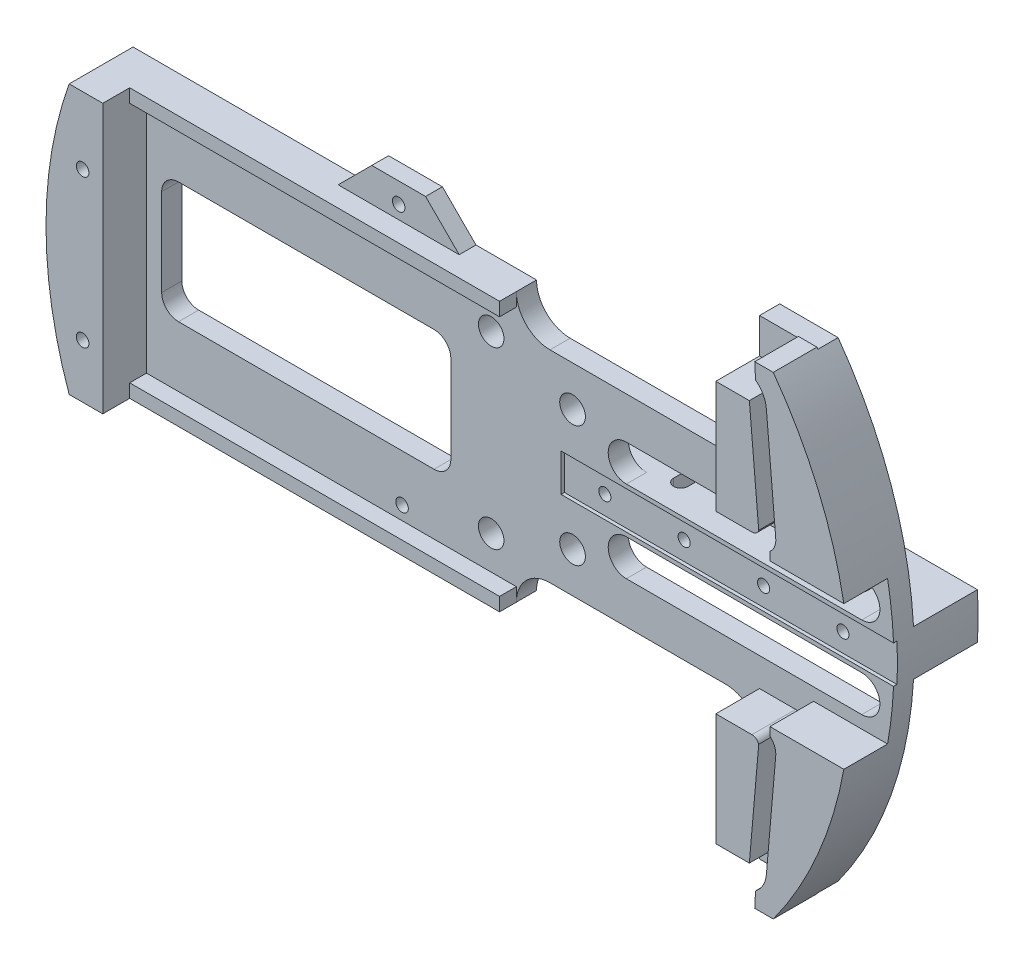
SolidWorks part; units mm, degrees
material "ABS"
ref_plane "Front Plane" through (0, 0, 0) normal (0, 0, 1) x (1, 0, 0)
ref_plane "Top Plane" through (0, 0, 0) normal (0, 1, 0) x (1, 0, 0)
ref_plane "Right Plane" through (0, 0, 0) normal (1, 0, 0) x (0, 0, -1)
sketch "Sketch1" plane through (0, 0, 0) normal (0, 0, 1) x (1, 0, 0)
  line L0 (0, 0) -> (91.8237, 0) construction
  line L1 (10.9774, 19.05) -> (44.196, 19.05)
  line L2 (-71.5726, 25.4) -> (4.6274, 25.4)
  line L3 (10.9774, -19.05) -> (44.196, -19.05)
  line L6 (50.546, 44.45) -> (61.5792, 44.45)
  line L7 (50.546, -44.45) -> (61.5792, -44.45)
  line L11 (-71.5726, -25.4) -> (4.6274, -25.4)
  line L12 (50.546, 25.4) -> (50.546, 44.45)
  line L14 (50.546, -25.4) -> (50.546, -44.45)
  arc A0 (61.5792, -44.45) -> (61.5792, 44.45) centre (0, 0) ccw
  circle A1 centre (0, 0) radius 75.946 construction
  arc A2 (-71.5726, 25.4) -> (-71.5726, -25.4) centre (0, 0) ccw
  arc A3 (44.196, 19.05) -> (50.546, 25.4) centre (44.196, 25.4) ccw
  arc A4 (10.9774, 19.05) -> (4.6274, 25.4) centre (10.9774, 25.4) cw
  arc A5 (44.196, -19.05) -> (50.546, -25.4) centre (44.196, -25.4) cw
  arc A6 (10.9774, -19.05) -> (4.6274, -25.4) centre (10.9774, -25.4) ccw
  point P6 (75.946, 0)
  point P17 (0, 0)
  dimension "D1" = 75.946
  dimension "D8" = 151.892
  dimension "D11" = 75.946
  dimension "D2" = 76.2
  dimension "D3" = 6.35
  dimension "D4" = 25.4
  dimension "D5" = 50.8
  dimension "D6" = 88.9
  dimension "D7" = 6.35
  dimension "D9" = 6.35
  dimension "D10" = 6.35
extrude "Boss-Extrude1" add sketch "Sketch1" along normal blind 3.81
sketch "Sketch2" plane through (0, 0, 3.81) normal (0, 0, 1) x (1, 0, 0)
  line L0 (60.2463, 17.78) -> (56.2059, 64.1603) construction
  line L1 (-13.9228, 0) -> (116.9939, 0) construction
  line L2 (35.7924, 17.78) -> (109.7023, 17.78) construction
  line L3 (61.8653, 17.78) -> (60.0951, 38.1)
  line L4 (58.6516, 17.5) -> (56.8815, 37.82)
  line L5 (56.8815, 37.82) -> (50.546, 37.82)
  line L6 (58.0471, 41.7789) -> (57.9008, 44.704)
  line L7 (57.9008, 44.704) -> (61.395, 44.704)
  line L8 (50.546, 37.82) -> (50.546, 16.5667)
  line L9 (50.546, 16.5667) -> (57.3661, 16.5667)
  line L10 (60.7595, 15.0941) -> (60.7595, 13.5449)
  line L11 (60.7595, 13.5449) -> (74.7284, 13.5449)
  line L12 (60.2463, -17.78) -> (56.2059, -64.1603) construction
  line L13 (60.7595, -13.5449) -> (74.7284, -13.5449)
  line L14 (60.7595, -15.0941) -> (60.7595, -13.5449)
  line L15 (50.546, -16.5667) -> (57.3661, -16.5667)
  line L16 (50.546, -37.82) -> (50.546, -16.5667)
  line L17 (57.9008, -44.704) -> (61.395, -44.704)
  line L18 (58.0471, -41.7789) -> (57.9008, -44.704)
  line L19 (56.8815, -37.82) -> (50.546, -37.82)
  line L20 (58.6516, -17.5) -> (56.8815, -37.82)
  line L21 (61.8653, -17.78) -> (60.0951, -38.1)
  line L22 (96.3863, 0) -> (96.3863, 82.276) construction
  arc A0 (61.5792, -44.45) -> (61.5792, 44.45) centre (0, 0) ccw construction
  arc A1 (60.0951, 38.1) -> (58.0471, 41.7789) centre (54.9639, 37.653) ccw
  arc A2 (57.3661, 16.5667) -> (58.6516, 17.5) centre (57.3661, 17.9187) ccw
  arc A3 (61.8653, 17.78) -> (60.7595, 15.0941) centre (58.7167, 17.5057) cw
  arc A4 (74.7284, 13.5449) -> (61.395, 44.704) centre (0, 0) ccw
  arc A5 (74.7284, -13.5449) -> (61.395, -44.704) centre (0, 0) cw
  arc A6 (61.8653, -17.78) -> (60.7595, -15.0941) centre (58.7167, -17.5057) ccw
  arc A7 (57.3661, -16.5667) -> (58.6516, -17.5) centre (57.3661, -17.9187) cw
  arc A8 (60.0951, -38.1) -> (58.0471, -41.7789) centre (54.9639, -37.653) cw
  point P0 (75.946, 0)
  point P1 (60.2463, 17.78)
  point P49 (96.3863, 44.704)
  dimension "D6" = 75.946
  dimension "D1" = 17.78
  dimension "D2" = 15.6997
  dimension "D3" = 85.021
  dimension "D4" = 1.6129
  dimension "D5" = 20.32
  dimension "D7" = 44.704
  dimension "D8" = 44.704
  dimension "D9" = 25.4
extrude "Boss-Extrude2" add sketch "Sketch2" along normal blind 8.255
sketch "Sketch3" plane through (0, 0, 3.81) normal (0, 0, 1) x (1, 0, 0)
  line L0 (-6.3906, 0) -> (92.2963, 0) construction
  line L2 (13.081, -3.55) -> (76.581, -3.55)
  line L3 (13.081, -3.55) -> (13.081, 3.55)
  line L4 (13.081, 3.55) -> (76.581, 3.55)
  line L5 (76.581, -3.55) -> (76.581, 3.55)
  line L6 (13.081, -3.55) -> (76.581, 3.55) construction
  line L7 (13.081, 3.55) -> (76.581, -3.55) construction
  line L8 (50.546, 16.5667) -> (50.546, 25.4) construction
  point P3 (44.831, 0)
  dimension "D1" = 7.1
  dimension "D2" = 63.5
  dimension "D3" = 37.465
extrude "Cut-Extrude1" cut sketch "Sketch3" against normal blind 0.635
sketch "Sketch6" plane through (0, 0, 0) normal (0, 0, -1) x (-1, 0, 0)
  line L1 (102.4877, 0) -> (-122.8054, 0) construction
sketch "Sketch7" plane through (0, 0, 0) normal (0, 0, 1) x (1, 0, 0)
  line L0 (0, 0) -> (107.1474, 0) construction
  line L1 (0, 0) -> (65.9911, 38.1) construction
  dimension "D1" = 30
ref_plane "Plane2" through (65.7712, 37.973, 0) normal (0.866, 0.5, 0) x (0, 0, -1)
sketch "Sketch9" plane through (0, 0, 3.81) normal (0, 0, 1) x (1, 0, 0)
  line L0 (-35.0108, 0) -> (91.9546, 0) construction
  line L1 (75.863, 3.55) -> (13.081, 3.55) construction
  line L2 (69.85, 11.17) -> (25.4, 11.17)
  line L3 (69.85, 11.17) -> (69.85, 4.312) construction
  line L4 (69.85, 4.312) -> (25.4, 4.312)
  line L5 (25.4, 11.17) -> (25.4, 4.312) construction
  line L6 (69.85, -4.312) -> (25.4, -4.312)
  line L7 (69.85, -11.17) -> (25.4, -11.17)
  arc A0 (25.4, 11.17) -> (25.4, 4.312) centre (25.4, 7.741) ccw
  arc A1 (69.85, 11.17) -> (69.85, 4.312) centre (69.85, 7.741) cw
  arc A2 (69.85, -11.17) -> (69.85, -4.312) centre (69.85, -7.741) ccw
  arc A3 (25.4, -11.17) -> (25.4, -4.312) centre (25.4, -7.741) cw
  point P9 (74.93, 0)
  dimension "D1" = 6.858
  dimension "D2" = 0.762
  dimension "D3" = 44.45
  dimension "D4" = 74.93
  dimension "D5" = 5.08
extrude "Cut-Extrude4" cut sketch "Sketch9" against normal through all
sketch "Sketch10" plane through (0, 0, 3.81) normal (0, 0, 1) x (1, 0, 0)
  line L0 (50.546, 37.82) -> (50.546, 16.5667) construction
  line L1 (-5.2199, 8.255) -> (-40.7011, 8.255) construction
  line L2 (-35.052, -6.0075) -> (-35.052, 31.8531) construction
  line L3 (-10.922, 11.43) -> (-59.182, 11.43)
  line L4 (-7.747, -8.255) -> (-7.747, 8.255)
  line L5 (-82.1806, 0) -> (28.287, 0) construction
  line L6 (-62.357, -8.255) -> (-62.357, 8.255)
  line L7 (-10.922, -11.43) -> (-59.182, -11.43)
  line L8 (-102.4877, 0) -> (122.8054, 0) construction
  arc A0 (-7.747, 8.255) -> (-10.922, 11.43) centre (-10.922, 8.255) ccw
  arc A1 (-62.357, 8.255) -> (-59.182, 11.43) centre (-59.182, 8.255) cw
  arc A2 (-7.747, -8.255) -> (-10.922, -11.43) centre (-10.922, -8.255) cw
  arc A3 (-62.357, -8.255) -> (-59.182, -11.43) centre (-59.182, -8.255) ccw
  point P0 (-35.052, 0)
  point P16 (-35.052, 15.5292)
  point P19 (-4.5185, 0)
  point P22 (-35.052, 11.43)
  point P24 (-65.5855, 0)
  dimension "D1" = 16.51
  dimension "D2" = 3.175
  dimension "D3" = 48.26
  dimension "D4" = 58.293
  dimension "D5" = 3.175
  dimension "D6" = 3.175
extrude "Cut-Extrude5" cut sketch "Sketch10" against normal through all
sketch "Sketch12" plane through (0, 0, 3.81) normal (0, 0, 1) x (1, 0, 0)
  line L0 (15.24, 51.8718) -> (15.24, -46.8025) construction
  line L1 (50.546, 37.82) -> (50.546, 16.5667) construction
  line L2 (0, 0) -> (87.8985, 0) construction
  line L3 (-102.4877, 0) -> (122.8054, 0) construction
  circle A0 centre (15.24, 11.43) radius 2.4257
  circle A1 centre (15.24, -11.43) radius 2.4257
  dimension "D2" = 4.8514
  dimension "D1" = 35.306
  dimension "D3" = 11.43
extrude "Cut-Extrude6" cut sketch "Sketch12" against normal through all
sketch "Sketch14" plane through (0, 0, 0) normal (0, 0, -1) x (-1, 0, 0)
  line L0 (28.1494, 0) -> (-118.1856, 0) construction
  line L1 (102.4877, 0) -> (-122.8054, 0) construction
  line L2 (-27.6293, 4.312) -> (-90.3941, 4.312) construction
  line L3 (-25.4, 4.312) -> (-69.85, 4.312) construction
  line L4 (-27.6293, -4.312) -> (-90.3941, -4.312) construction
  line L6 (-69.85, -4.312) -> (-25.4, -4.312) construction
  line L7 (-75.8235, 4.312) -> (7.747, 4.312)
  line L8 (7.747, -8.255) -> (7.747, 8.255) construction
  line L9 (7.747, 4.312) -> (7.747, -4.312)
  line L10 (7.747, -4.312) -> (-75.8235, -4.312)
  arc A0 (-75.8235, 4.312) -> (-75.8235, -4.312) centre (0, 0) ccw
  arc A1 (-61.5792, 44.45) -> (-61.5792, -44.45) centre (0, 0) ccw construction
extrude "Boss-Extrude3" add sketch "Sketch14" along normal blind 12.065
sketch "Sketch4" plane through (0, 0, 3.175) normal (0, 0, 1) x (1, 0, 0)
  line L0 (13.081, 3.55) -> (13.081, -3.55) construction
  line L1 (-1.4827, 0) -> (103.4049, 0) construction
  circle A0 centre (20.701, 0) radius 1.143
  circle A1 centre (35.687, 0) radius 1.143
  circle A2 centre (50.673, 0) radius 1.143
  circle A3 centre (65.659, 0) radius 1.143
  point P2 (13.081, 0)
  dimension "D2" = 2.286
  dimension "D1" = 7.62
  dimension "D3" = 4
extrude "Cut-Extrude2" cut sketch "Sketch4" against normal blind 11.43
sketch "Sketch15" plane through (0, 4.312, 0) normal (0, 1, 0) x (1, 0, 0)
  line L0 (50.546, -12.065) -> (50.546, 20.3871) construction
  line L1 (30.2514, -23.2535) -> (30.2514, 35.9942) construction
  line L2 (39.751, -23.2535) -> (39.751, 35.9942) construction
  line L3 (28.8925, 1.6157) -> (28.8925, 5.9337)
  line L5 (28.8925, 3.7747) -> (33.0146, 3.7747) construction
  line L6 (31.6103, 1.6157) -> (31.6103, 5.9337)
  line L7 (35.0012, 35.9942) -> (35.0012, -23.2535) construction
  line L8 (41.1099, 1.6157) -> (41.1099, 5.9337)
  line L9 (38.3921, 1.6157) -> (38.3921, 5.9337)
  line L10 (54.737, -17.6697) -> (54.737, 24.0892) construction
  line L11 (47.244, -27.3174) -> (47.244, 51.8804) construction
  line L12 (65.5955, 1.6157) -> (65.5955, 5.9337)
  line L13 (62.8777, 1.6157) -> (62.8777, 5.9337)
  line L14 (56.0959, 1.6157) -> (56.0959, 5.9337)
  line L15 (53.3781, 1.6157) -> (53.3781, 5.9337)
  arc A0 (28.8925, 1.6157) -> (31.6103, 1.6157) centre (30.2514, 1.6157) ccw
  arc A1 (28.8925, 5.9337) -> (31.6103, 5.9337) centre (30.2514, 5.9337) cw
  arc A2 (41.1099, 5.9337) -> (38.3921, 5.9337) centre (39.751, 5.9337) ccw
  arc A3 (41.1099, 1.6157) -> (38.3921, 1.6157) centre (39.751, 1.6157) cw
  arc A4 (65.5955, 5.9337) -> (62.8777, 5.9337) centre (64.2366, 5.9337) ccw
  arc A5 (65.5955, 1.6157) -> (62.8777, 1.6157) centre (64.2366, 1.6157) cw
  arc A6 (53.3781, 1.6157) -> (56.0959, 1.6157) centre (54.737, 1.6157) ccw
  arc A7 (53.3781, 5.9337) -> (56.0959, 5.9337) centre (54.737, 5.9337) cw
  dimension "D1" = 20.2946
  dimension "D2" = 9.4996
  dimension "D3" = 2.7178
  dimension "D4" = 4.7498
  dimension "D5" = 4.318
  dimension "D6" = 4.191
  dimension "D7" = 7.493
extrude "Cut-Extrude7" cut sketch "Sketch15" against normal through all
sketch "Sketch16" plane through (0, -4.312, 0) normal (0, -1, 0) x (1, 0, 0)
  line L0 (75.8235, -12.065) -> (-7.747, -12.065) construction
  line L1 (4.6274, 0) -> (-7.747, 0)
  line L2 (0, -12.065) -> (22.5475, -12.065)
  line L4 (-7.747, 0) -> (-7.747, -12.065)
  line L5 (-7.747, -12.065) -> (0, -12.065)
  arc A0 (4.6274, 0) -> (22.5475, -12.065) centre (-11.8904, -43.8745) cw
extrude "Cut-Extrude8" cut sketch "Sketch16" against normal through all and the other way through all
sketch "Sketch17" plane through (0, 0, 3.81) normal (0, 0, 1) x (1, 0, 0)
  line L0 (-87.521, 0) -> (99.4626, 0) construction
  line L1 (-102.4877, 0) -> (122.8054, 0) construction
  line L3 (-0.127, 0) -> (-0.127, 33.8266) construction
  line L5 (-7.747, -8.255) -> (-7.747, 8.255) construction
  circle A0 centre (-0.127, 16.51) radius 2.413
  circle A2 centre (-0.127, -16.51) radius 2.413
  dimension "D1" = 4.826
  dimension "D2" = 16.51
  dimension "D3" = 7.62
extrude "Cut-Extrude9" cut sketch "Sketch17" against normal through all
sketch "Sketch19" plane through (0, 0, 3.81) normal (0, 0, 1) x (1, 0, 0)
  line L0 (-71.5726, -25.4) -> (4.6274, -25.4) construction
  line L3 (-71.5726, -25.4) -> (-65.2226, -25.4)
  line L4 (-65.2226, -25.4) -> (-65.2226, 25.4)
  line L5 (4.6274, 25.4) -> (-71.5726, 25.4) construction
  line L6 (-65.2226, 25.4) -> (-71.5726, 25.4)
  circle A0 centre (0, 0) radius 75.946 construction
  arc A3 (-71.5726, 25.4) -> (-71.5726, -25.4) centre (0, 0) ccw
  point P0 (-65.2226, -25.4)
  point P6 (-71.5726, -25.4)
  dimension "D2" = 151.892
  dimension "D1" = 6.35
extrude "Boss-Extrude5" add sketch "Sketch19" along normal blind 8.255
sketch "Sketch20" plane through (0, -25.4, 0) normal (0, -1, 0) x (1, 0, 0)
  line L0 (-65.2226, 3.81) -> (4.6274, 3.81)
  line L1 (4.6274, 3.81) -> (4.6274, 6.985)
  line L2 (4.6274, 6.985) -> (-65.2226, 6.985)
  line L3 (-65.2226, 12.065) -> (-65.2226, 3.81) construction
  line L4 (-65.2226, 6.985) -> (-65.2226, 3.81)
  dimension "D1" = 3.175
extrude "Boss-Extrude6" add sketch "Sketch20" against normal blind 2.54
mirror "Mirror1" about plane through (0, 0, 0) normal (0, 1, 0) of "Boss-Extrude6"
sketch "Sketch21" plane through (0, 0, 0) normal (0, 0, -1) x (-1, 0, 0)
  line L0 (6.8026, 25.4) -> (13.1526, 31.75)
  line L1 (-4.6274, 25.4) -> (71.5726, 25.4) construction
  line L2 (13.1526, 31.75) -> (23.3126, 31.75)
  line L3 (23.3126, 31.75) -> (29.6626, 25.4)
  line L4 (6.8026, 25.4) -> (29.6626, 25.4)
  dimension "D1" = 45
  dimension "D2" = 45
  dimension "D3" = 6.35
  dimension "D4" = 10.16
  dimension "D5" = 11.43
extrude "Boss-Extrude7" add sketch "Sketch21" against normal blind 3.175
sketch "Sketch22" plane through (0, 0, 0) normal (0, 0, -1) x (-1, 0, 0)
  line L0 (18.2326, 31.75) -> (18.2326, -52.9664) construction
  line L1 (23.3126, 31.75) -> (13.1526, 31.75) construction
  circle A0 centre (18.2326, 27.94) radius 1.1874
  circle A1 centre (16.9626, -20.3033) radius 1.1874
  circle A2 centre (69.0326, 12.7) radius 1.1875
  circle A3 centre (69.0326, -15.24) radius 1.1875
  dimension "D1" = 2.3749
  dimension "D2" = 2.3749
  dimension "D3" = 48.26
  dimension "D4" = 3.81
  dimension "D5" = 2.3749
  dimension "D6" = 15.24
  dimension "D7" = 50.8
  dimension "D8" = 2.3749
  dimension "D9" = 27.94
  dimension "D10" = 1.27
extrude "Cut-Extrude10" cut sketch "Sketch22" against normal through all
equation "\"0.15inin\"=0.2"
equation "\"0.45inin\"=0.35"
equation "\"0.55inin\"=0.45"
equation "\"0.125inin\"=0.325"
